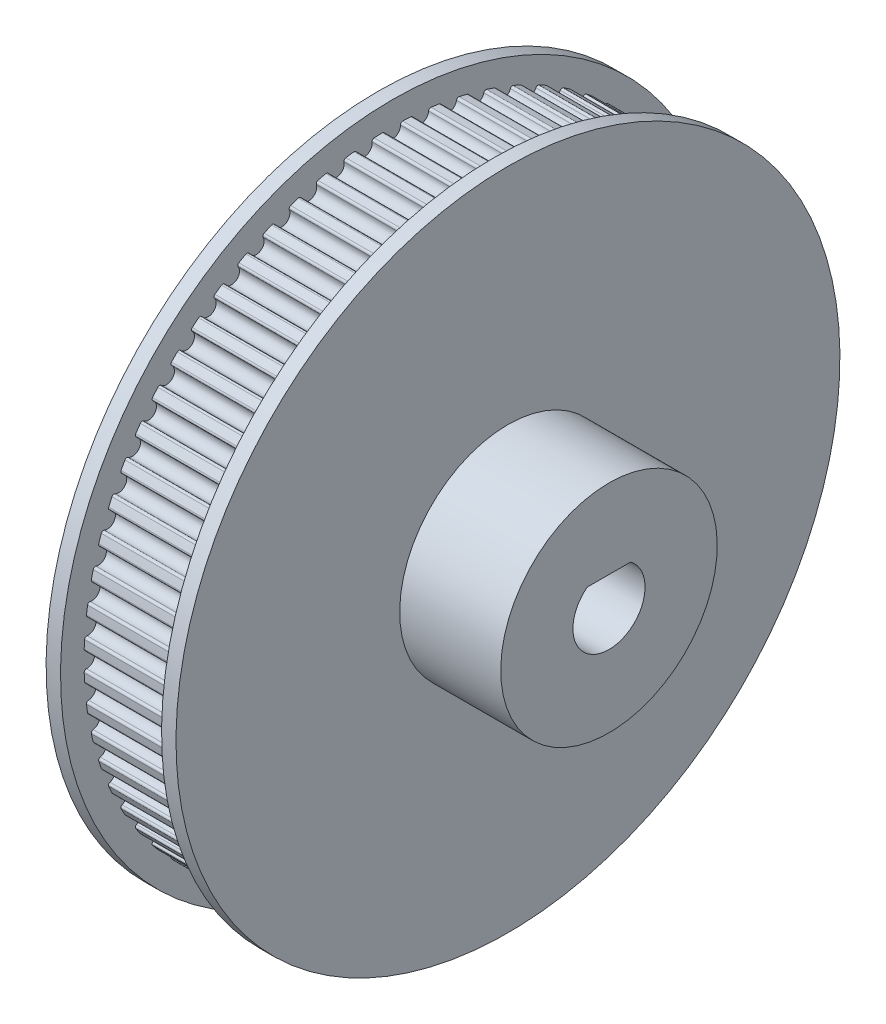
SolidWorks part; units mm, degrees
ref_plane "Front Plane" through (0, 0, 0) normal (0, 0, 1) x (1, 0, 0)
ref_plane "Top Plane" through (0, 0, 0) normal (0, 1, 0) x (1, 0, 0)
ref_plane "Right Plane" through (0, 0, 0) normal (1, 0, 0) x (0, 0, -1)
sketch "Sketch1" plane through (0, 0, 0) normal (0, 0, 1) x (1, 0, 0)
  line L0 (0, 0) -> (-7, 0)
  line L1 (-7, 0) -> (-16, 0)
  line L2 (-16, 0) -> (-16, 23)
  line L3 (-16, 23) -> (-15, 23)
  line L4 (-15, 23) -> (-15, 21.37)
  line L5 (-15, 21.37) -> (-8, 21.37)
  line L6 (-8, 21.37) -> (-8, 23)
  line L7 (-8, 23) -> (-7, 23)
  line L8 (-7, 23) -> (-7, 0)
  line L9 (0, 0) -> (0, 7.5)
  line L10 (0, 7.5) -> (-7, 7.5)
  dimension "D1" = 7
  dimension "D2" = 9
  dimension "D3" = 23
  dimension "D4" = 1
  dimension "D5" = 1.63
  dimension "D6" = 7
  dimension "D7" = 1
  dimension "D8" = 1.63
  dimension "D9" = 7.5
revolve "Revolve1" add sketch "Sketch1" angle 360 about L1
sketch "Sketch2" plane through (-16, 0, 0) normal (-1, 0, 0) x (0, 0, 1)
  line L1 (0, 2) -> (1.5, 2)
  line L2 (0, 2) -> (-1.5, 2)
  arc A0 (-1.5, 2) -> (1.5, 2) centre (0, 0) ccw
  dimension "D1" = 5
  dimension "D2" = 1.5
  dimension "D3" = 1.5
sketch "Sketch3" plane through (-8, 0, 0) normal (-1, 0, 0) x (0, 0, 1)
  arc A2 (0.5184, 21.3637) -> (-0.5184, 21.3637) centre (0, 0) ccw
  arc A3 (-0.5184, 21.3637) -> (0.5184, 21.3637) centre (0, 21.18) ccw
extrude "Cut-Extrude2" cut sketch "Sketch3" along normal blind 7
fillet "Fillet1" radius 0.15 2 edges at (-11.5, 21.3637, -0.5184) (-11.5, 21.3637, 0.5184)
pattern_circular "CirPattern1" count 68 over 360 about axis through (0, 0, 0) along (1, 0, 0) of "Cut-Extrude2", "Fillet1"
extrude "Cut-Extrude3" cut sketch "Sketch2" against normal through all both and the other way through all
